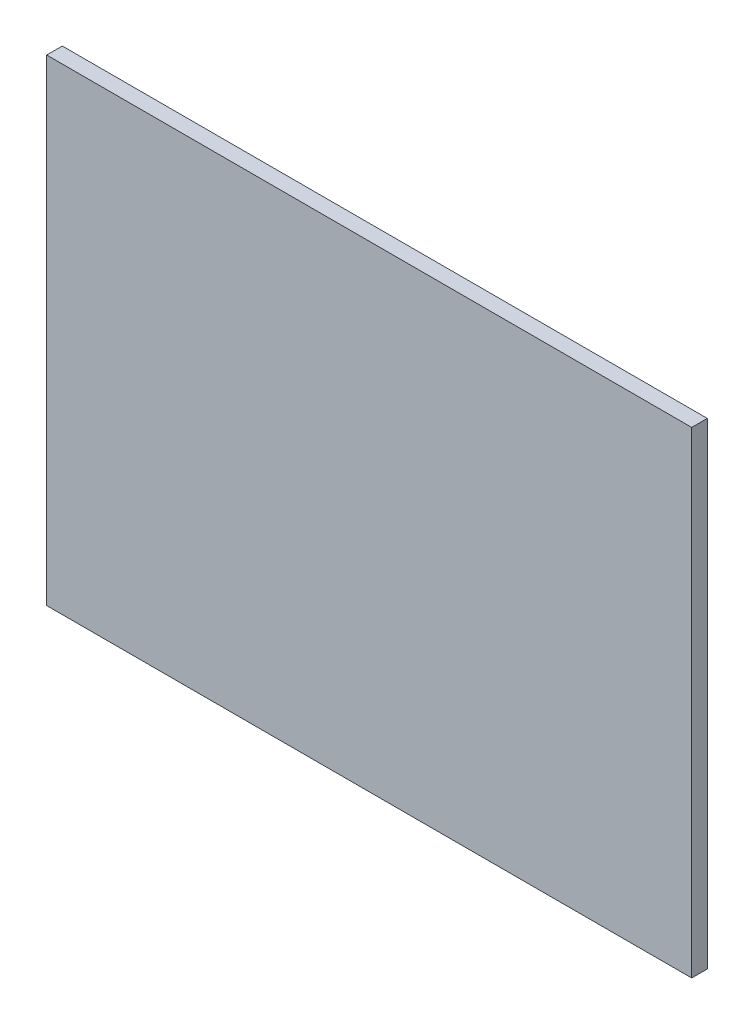
SolidWorks part; units mm, degrees
ref_plane "Front Plane" through (0, 0, 0) normal (0, 0, 1) x (1, 0, 0)
ref_plane "Top Plane" through (0, 0, 0) normal (0, 1, 0) x (1, 0, 0)
ref_plane "Right Plane" through (0, 0, 0) normal (1, 0, 0) x (0, 0, -1)
sketch "Sketch1" plane through (0, 0, 0) normal (0, 0, 1) x (1, 0, 0)
  line L1 (372, -275) -> (-372, -275)
  line L2 (372, -275) -> (372, 275)
  line L3 (372, 275) -> (-372, 275)
  line L4 (-372, -275) -> (-372, 275)
  line L5 (372, -275) -> (-372, 275) construction
  line L6 (372, 275) -> (-372, -275) construction
  point P0 (0, 0)
  dimension "D1" = 550
  dimension "D2" = 744
extrude "Boss-Extrude1" add sketch "Sketch1" along normal blind 18
equation "\"H_DSP\"=18"
equation "\"D1@Boss-Extrude1\"=\"H_DSP\""
